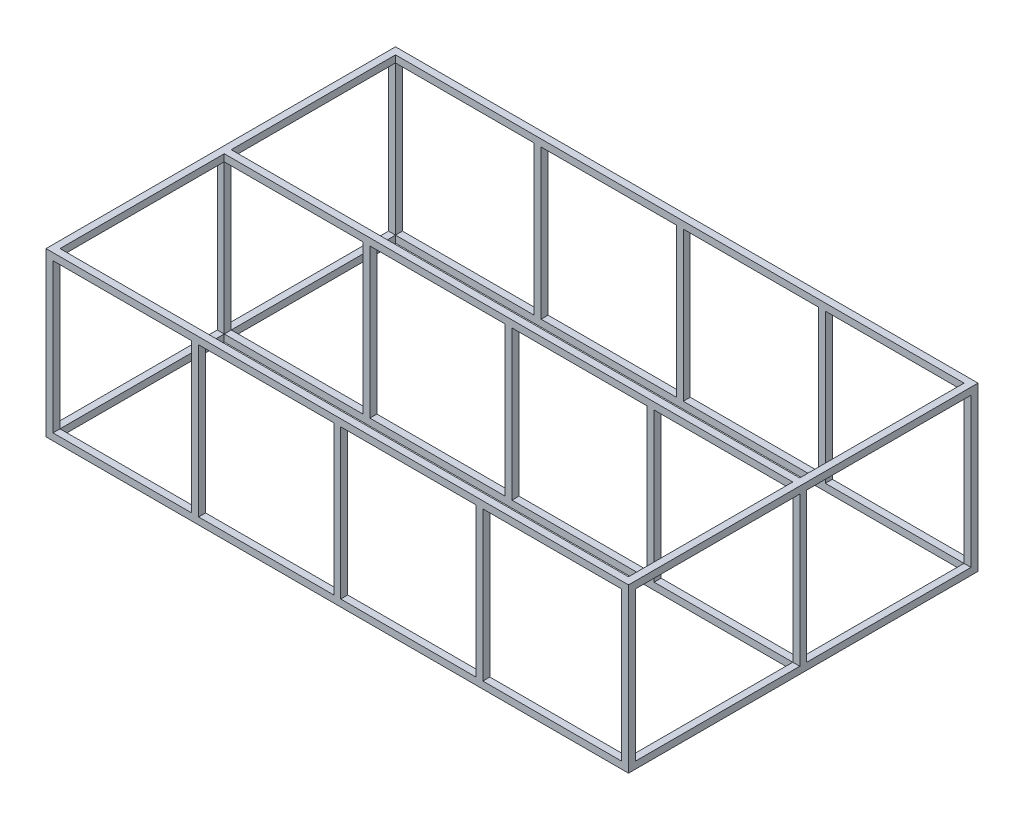
SolidWorks part; units mm, degrees
ref_plane "Front Plane" through (0, 0, 0) normal (0, 0, 1) x (1, 0, 0)
ref_plane "Top Plane" through (0, 0, 0) normal (0, 1, 0) x (1, 0, 0)
ref_plane "Right Plane" through (0, 0, 0) normal (1, 0, 0) x (0, 0, -1)
sketch "Sketch1" plane through (0, 0, 0) normal (0, 0, 1) x (1, 0, 0)
  line L0 (30, 0) -> (30, 700) construction
  line L1 (0, 0) -> (2500, 0)
  line L2 (0, 0) -> (0, 700)
  line L3 (0, 700) -> (2500, 700)
  line L4 (2500, 0) -> (2500, 700)
  line L5 (0, 30) -> (2500, 30) construction
  line L6 (0, 350) -> (2500, 350) construction
  line L7 (1250, 700) -> (1250, 0) construction
  line L8 (2470, 0) -> (2470, 700) construction
  line L9 (0, 670) -> (2500, 670) construction
  line L11 (30, 30) -> (2470, 30)
  line L12 (30, 30) -> (30, 670)
  line L13 (30, 670) -> (2470, 670)
  line L14 (2470, 30) -> (2470, 670)
  point P9 (30, 30)
  dimension "D1" = 2500
  dimension "D2" = 700
  dimension "D3" = 30
  dimension "D4" = 30
extrude "Boss-Extrude1" add sketch "Sketch1" along normal blind 1500
sketch "Sketch2" plane through (0, 700, 0) normal (0, 1, 0) x (1, 0, 0)
  line L0 (1250, 0) -> (1250, -1500) construction
  line L1 (2500, 0) -> (0, 0) construction
  line L2 (2500, -1500) -> (0, -1500) construction
  line L3 (0, -750) -> (2500, -750) construction
  line L4 (0, -1500) -> (0, 0) construction
  line L5 (2500, -1500) -> (2500, 0) construction
  line L6 (30, -1500) -> (30, 0) construction
  line L7 (0, -1470) -> (2500, -1470) construction
  line L8 (2470, -1500) -> (2470, 0) construction
  line L9 (0, -30) -> (2500, -30) construction
  line L11 (30, -1470) -> (2470, -1470)
  line L12 (30, -1470) -> (30, -30)
  line L13 (30, -30) -> (2470, -30)
  line L14 (2470, -1470) -> (2470, -30)
  dimension "D1" = 30
  dimension "D2" = 30
  dimension "D3" = 30
  dimension "D4" = 30
extrude "Cut-Extrude1" cut sketch "Sketch2" against normal blind 1500 contours L12 L11 L14 L13
sketch "Sketch3" plane through (2500, 0, 0) normal (1, 0, 0) x (0, 0, -1)
  line L0 (-1500, 0) -> (0, 0) construction
  line L1 (-1470, 30) -> (-30, 30)
  line L2 (-1470, 30) -> (-1470, 670)
  line L3 (-1470, 670) -> (-30, 670)
  line L4 (-30, 30) -> (-30, 670)
  line L5 (-1500, 0) -> (-1500, 700) construction
  line L6 (0, 0) -> (0, 700) construction
  line L7 (-1500, 700) -> (0, 700) construction
  point P8 (0, 0)
  point P9 (0, 0)
  dimension "D1" = 30
  dimension "D2" = 30
  dimension "D3" = 30
  dimension "D4" = 30
extrude "Cut-Extrude2" cut sketch "Sketch3" against normal blind 3595
ref_plane "Plane1" through (30, 30, 1470) normal (1, 0, 0) x (0, 0, -1)
sketch "Sketch5" plane through (0, 30, 0) normal (0, 1, 0) x (1, 0, 0)
  line L0 (30, -1470) -> (1250, -1470) construction
  line L1 (30, -1470) -> (2470, -1470) construction
  line L2 (30, -1500) -> (2470, -1500) construction
  line L3 (640, -1470) -> (625, -1470)
  line L4 (640, -1470) -> (640, -1500)
  line L5 (640, -1500) -> (625, -1500)
  line L6 (625, -1470) -> (625, -1500)
  line L7 (1250, -1470) -> (1250, -1500) construction
  line L8 (640, -1500) -> (655, -1500)
  line L9 (640, -1500) -> (640, -1470)
  line L10 (640, -1470) -> (655, -1470)
  line L11 (655, -1500) -> (655, -1470)
  line L12 (1860, -1500) -> (1875, -1500)
  line L13 (1875, -1470) -> (1875, -1500)
  line L14 (1860, -1470) -> (1875, -1470)
  line L15 (1860, -1470) -> (1860, -1500)
  line L16 (1860, -1470) -> (1845, -1470)
  line L17 (1845, -1500) -> (1845, -1470)
  line L18 (1860, -1500) -> (1845, -1500)
  line L19 (1860, -1500) -> (1860, -1470)
  line L20 (30, -750) -> (2470, -750) construction
  line L21 (30, -1470) -> (30, -30) construction
  line L22 (2470, -30) -> (2470, -1470) construction
  line L23 (1860, 0) -> (1845, 0)
  line L24 (1250, -1470) -> (1235, -1470)
  line L25 (1250, -1470) -> (1250, -1500)
  line L26 (1250, -1500) -> (1235, -1500)
  line L27 (1235, -1470) -> (1235, -1500)
  line L28 (1250, -1500) -> (1265, -1500)
  line L29 (1250, -1500) -> (1250, -1470)
  line L30 (1250, -1470) -> (1265, -1470)
  line L31 (1265, -1500) -> (1265, -1470)
  line L32 (1860, 0) -> (1875, 0)
  line L33 (1875, -30) -> (1875, 0)
  line L34 (1860, -30) -> (1875, -30)
  line L35 (1860, -30) -> (1845, -30)
  line L36 (1845, 0) -> (1845, -30)
  line L37 (1250, -30) -> (1265, -30)
  line L38 (1265, 0) -> (1265, -30)
  line L39 (1250, 0) -> (1265, 0)
  line L40 (1250, 0) -> (1250, -30)
  line L41 (1250, 0) -> (1235, 0)
  line L42 (1235, -30) -> (1235, 0)
  line L43 (1250, -30) -> (1235, -30)
  line L44 (1250, -30) -> (1250, 0)
  line L45 (640, -30) -> (655, -30)
  line L46 (655, 0) -> (655, -30)
  line L47 (640, 0) -> (655, 0)
  line L48 (640, 0) -> (640, -30)
  line L49 (640, 0) -> (625, 0)
  line L50 (625, -30) -> (625, 0)
  line L51 (640, -30) -> (625, -30)
  line L52 (640, -30) -> (640, 0)
  line L54 (1845, -1500) -> (1875, -1500)
  line L55 (1845, -1500) -> (1845, -1470)
  line L56 (1845, -1470) -> (1875, -1470)
  line L57 (1875, -1500) -> (1875, -1470)
  line L58 (1845, -30) -> (1875, -30)
  line L59 (1845, -30) -> (1845, 0)
  line L60 (1845, 0) -> (1875, 0)
  line L61 (1875, -30) -> (1875, 0)
  point P5 (640, -1470)
  line M26 (2470, -1470) -> (30, -1470)
  line M28 (30, -1500) -> (2470, -1500)
  dimension "D3" = 15
  dimension "D4" = 15
extrude "Boss-Extrude3" add sketch "Sketch5" along normal blind 640 contours L51 L48 L49 L50 | L47 L48 L45 L46 | L43 L40 L41 L42 | L39 L40 L37 L38 | L23 L36 L35 L34 L33 L32 | L17 L15 M28 M26 | L15 L13 M26 M28 | L27 L25 M26 M28 | L31 L25 M28 M26 | L11 L4 M28 M26 | L6 L4 M26 M28
sketch "Sketch7" plane through (30, 0, 0) normal (1, 0, 0) x (0, 0, -1)
  line L0 (-1470, 15) -> (-30, 15) construction
  line L1 (-1470, 0) -> (-1470, 30) construction
  line L2 (-30, 0) -> (-30, 30) construction
  line L3 (-1470, 30) -> (-30, 30) construction
  line L4 (-735, 0) -> (-765, 0)
  line L5 (-735, 0) -> (-735, 30)
  line L6 (-735, 30) -> (-765, 30)
  line L7 (-765, 0) -> (-765, 30)
  line L8 (-735, 0) -> (-765, 30) construction
  line L9 (-735, 30) -> (-765, 0) construction
  line L10 (-1470, 685) -> (-30, 685) construction
  line L11 (-1470, 670) -> (-1470, 700) construction
  line L12 (-30, 670) -> (-30, 700) construction
  line L13 (-1470, 700) -> (-30, 700) construction
  line L14 (-735, 670) -> (-765, 670)
  line L15 (-735, 670) -> (-735, 700)
  line L16 (-735, 700) -> (-765, 700)
  line L17 (-765, 670) -> (-765, 700)
  line L18 (-735, 670) -> (-765, 700) construction
  line L19 (-735, 700) -> (-765, 670) construction
  point P6 (-750, 15)
  point P19 (-750, 685)
  dimension "D1" = 30
  dimension "D2" = 30
extrude "Boss-Extrude4" add sketch "Sketch7" along normal up to next
sketch "Sketch8" plane through (0, 30, 0) normal (0, 1, 0) x (1, 0, 0)
  line L0 (2485, -1470) -> (2485, -30) construction
  line L1 (2470, -1470) -> (2500, -1470) construction
  line L2 (2470, -30) -> (2500, -30) construction
  line L3 (15, -1470) -> (15, -30) construction
  line L4 (0, -1470) -> (30, -1470) construction
  line L5 (0, -30) -> (30, -30) construction
  line L6 (2470, -765) -> (30, -765) construction
  line L7 (2500, -735) -> (2470, -735)
  line L8 (2500, -735) -> (2500, -765)
  line L9 (2500, -765) -> (2470, -765)
  line L10 (2470, -735) -> (2470, -765)
  line L11 (2500, -735) -> (2470, -765) construction
  line L12 (2500, -765) -> (2470, -735) construction
  line L13 (2470, -765) -> (2470, -1470) construction
  line L14 (0, -1470) -> (0, -30) construction
  line L15 (30, -765) -> (0, -765)
  line L16 (30, -765) -> (30, -735)
  line L17 (30, -735) -> (0, -735)
  line L18 (0, -765) -> (0, -735)
  line L19 (30, -765) -> (0, -735) construction
  line L20 (30, -735) -> (0, -765) construction
  line L21 (655, -1470) -> (655, -765) construction
  line L22 (1265, -1470) -> (1265, -765) construction
  line L23 (1875, -1470) -> (1875, -765) construction
  line L24 (2470, -735) -> (30, -735) construction
  line L25 (655, -765) -> (625, -765)
  line L26 (655, -765) -> (655, -735)
  line L27 (655, -735) -> (625, -735)
  line L28 (625, -765) -> (625, -735)
  line L30 (1265, -765) -> (1235, -765)
  line L31 (1265, -765) -> (1265, -735)
  line L32 (1265, -735) -> (1235, -735)
  line L33 (1235, -765) -> (1235, -735)
  line L34 (1875, -765) -> (1845, -765)
  line L35 (1875, -765) -> (1875, -735)
  line L36 (1875, -735) -> (1845, -735)
  line L37 (1845, -765) -> (1845, -735)
  point P12 (2485, -750)
  point P21 (15, -750)
  dimension "D1" = 30
  dimension "D2" = 30
  dimension "D3" = 30
extrude "Boss-Extrude5" add sketch "Sketch8" along normal blind 640
